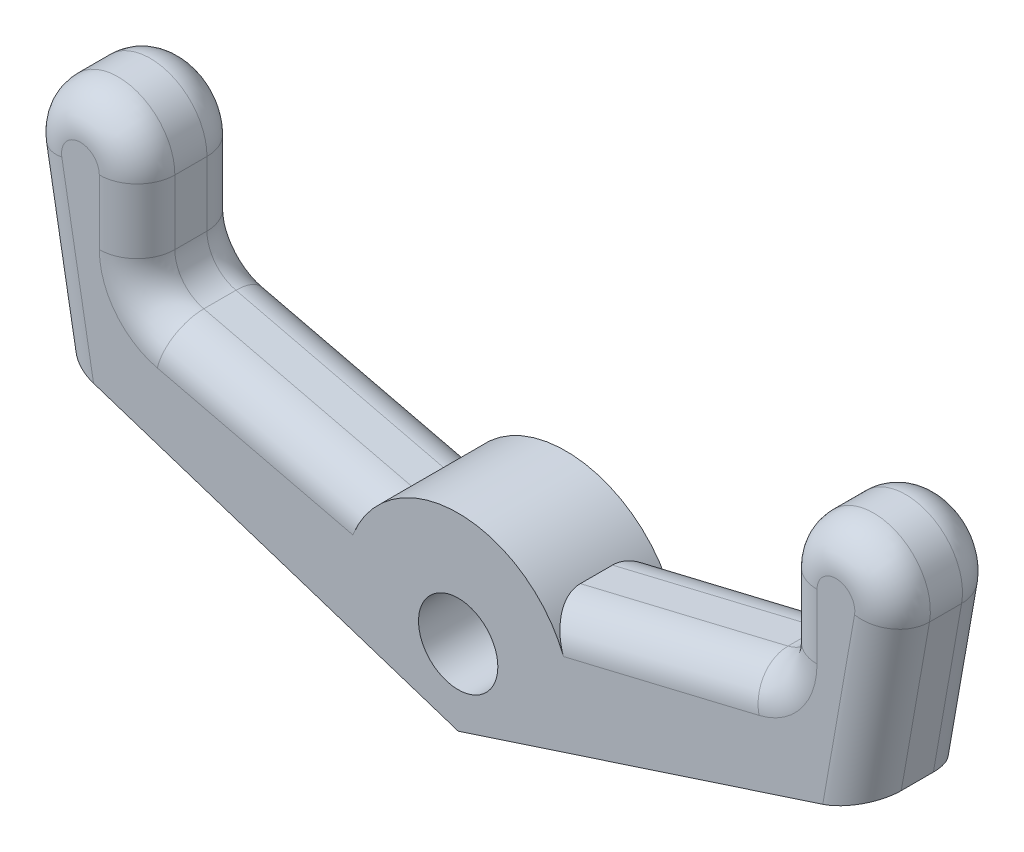
SolidWorks part; units mm, degrees
ref_plane "Front Plane" through (0, 0, 0) normal (0, 0, 1) x (1, 0, 0)
ref_plane "Top Plane" through (0, 0, 0) normal (0, 1, 0) x (1, 0, 0)
ref_plane "Right Plane" through (0, 0, 0) normal (1, 0, 0) x (0, 0, -1)
sketch "Sketch1" plane through (0, 0, 0) normal (0, 0, 1) x (1, 0, 0)
  line L0 (0, 0) -> (0, 4.534) construction
  line L1 (2.2361, 2) -> (8.5, 3.5)
  line L2 (8.5, 3.5) -> (8.5, 6)
  line L3 (11.4772, 5.7395) -> (10.7297, 1.5)
  line L4 (10.7297, 1.5) -> (0, -2)
  line L5 (-10.7297, 1.5) -> (0, -2)
  line L6 (-11.4772, 5.7395) -> (-10.7297, 1.5)
  line L7 (-8.5, 3.5) -> (-8.5, 6)
  line L8 (-2.2361, 2) -> (-8.5, 3.5)
  circle A0 centre (0, 0) radius 1.05
  arc A1 (8.5, 6) -> (11.4772, 5.7395) centre (10, 6) cw
  arc A2 (-2.2361, 2) -> (2.2361, 2) centre (0, 0) cw
  arc A3 (-8.5, 6) -> (-11.4772, 5.7395) centre (-10, 6) ccw
  dimension "D1" = 2.1
  dimension "D4" = 1.5
  dimension "D6" = 10
  dimension "D5" = 3
  dimension "D2" = 2
  dimension "D3" = 6
  dimension "D7" = 2.5
  dimension "D8" = 4.5
  dimension "D9" = 10
  dimension "D10" = 2
extrude "Boss-Extrude1" add sketch "Sketch1" along normal blind 2.85
fillet "Fillet2" radius 1 2 edges at (8.5, 3.5, 1.425) (-8.5, 3.5, 1.425)
fillet "Fillet1" radius 1 20 edges at (11.1034, 3.6198, 2.85) (8.5, 5.1444, 2.85) (11.1034, 3.6198, 0) (8.5, 5.1444, 0) (10.1307, 7.4943, 2.85) (10.1307, 7.4943, 0) (4.9845, 2.6582, 2.85) (8.2851, 3.6695, 2.85) (4.9845, 2.6582, 0) (8.2851, 3.6695, 0) (-4.9845, 2.6582, 0) (-8.2851, 3.6695, 0) (-8.5, 5.1444, 0) (-11.1034, 3.6198, 0) (-4.9845, 2.6582, 2.85) (-8.2851, 3.6695, 2.85) (-8.5, 5.1444, 2.85) (-11.1034, 3.6198, 2.85) (-10.1307, 7.4943, 0) (-10.1307, 7.4943, 2.85)
